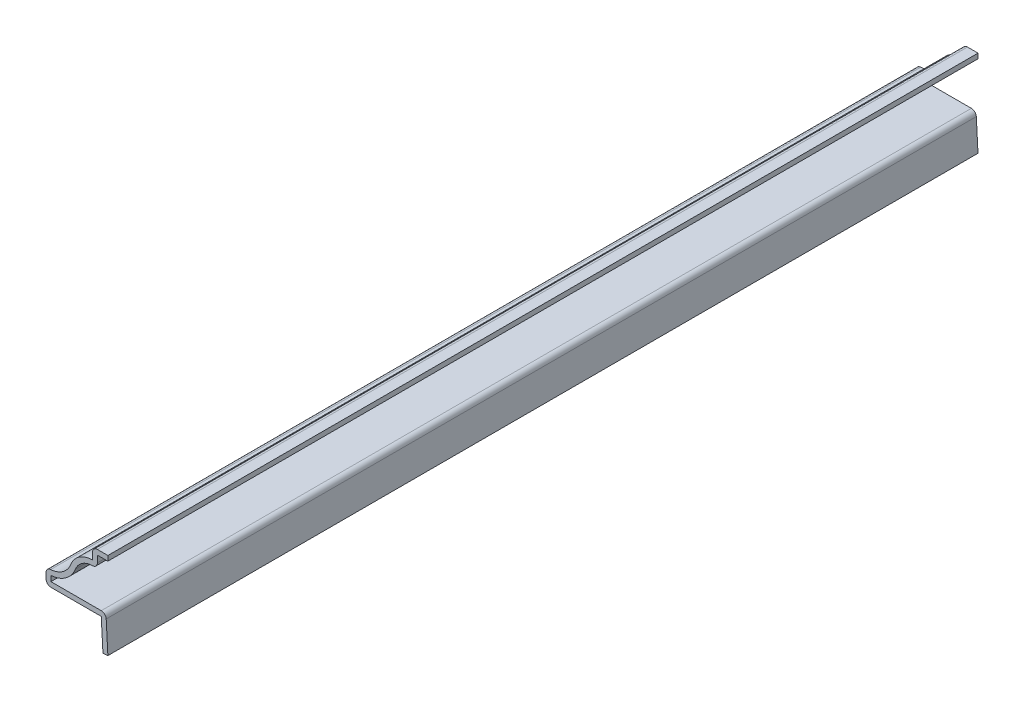
SolidWorks part; units mm, degrees
ref_plane "Front Plane" through (0, 0, 0) normal (0, 0, 1) x (1, 0, 0)
ref_plane "Top Plane" through (0, 0, 0) normal (0, 1, 0) x (1, 0, 0)
ref_plane "Right Plane" through (0, 0, 0) normal (1, 0, 0) x (0, 0, -1)
sketch "Sketch1" plane through (0, 0, 0) normal (0, 0, 1) x (1, 0, 0)
  line L0 (0, 0) -> (0, 17.8594) construction
  line L1 (0, 17.8594) -> (-3.175, 17.8594)
  line L2 (-3.175, 17.8594) -> (-3.175, 15.4781)
  line L3 (-12.7, 9.525) -> (-12.7, 6.35)
  line L4 (-12.7, 6.35) -> (-1.3592, 6.35)
  line L5 (-1.3592, 6.35) -> (-1.0145, 0)
  line L6 (-0.3969, 7.366) -> (0, 0.0551) construction
  line L7 (-0.3447, 6.4051) -> (0.1717, -3.1071) construction
  line L8 (-1.3592, 6.35) -> (-0.8428, -3.1622) construction
  line L9 (-12.7, 7.366) -> (-1.3592, 7.366) construction
  line L10 (-0.3969, 7.366) -> (-1.3592, 7.366) construction
  line L11 (-1.0145, 0) -> (0, 0.0551) construction
  arc A0 (-3.175, 15.4781) -> (-7.5996, 12.4775) centre (-3.175, 10.7156) ccw
  arc A1 (-7.5996, 12.4775) -> (-12.7, 9.525) centre (-12.0243, 14.2393) cw
  point P2 (0, 0)
  point P19 (0.0014, 0.0552)
  dimension "D10" = 4.7625
  dimension "D1" = 12.7
  dimension "D2" = 11.5094
  dimension "D3" = 6.35
  dimension "D5" = 0.3969
  dimension "D6" = 3.175
  dimension "D7" = 2.3813
  dimension "D8" = 9.525
  dimension "D9" = 3.175
  dimension "D4" = 1.016
  dimension "D11" = 1.016
extrude "Extrude-Thin1" add sketch "Sketch1" against normal blind 178.5938 thin thin type one direction reverse wall 1.016
fillet "Fillet1" radius 1.016 5 edges at (-0.3969, 7.366, -89.2969) (-12.7, 6.35, -89.2969) (-12.7, 9.525, -89.2969) (-2.159, 14.3217, -89.2969) (-3.175, 17.8594, -89.2969)
